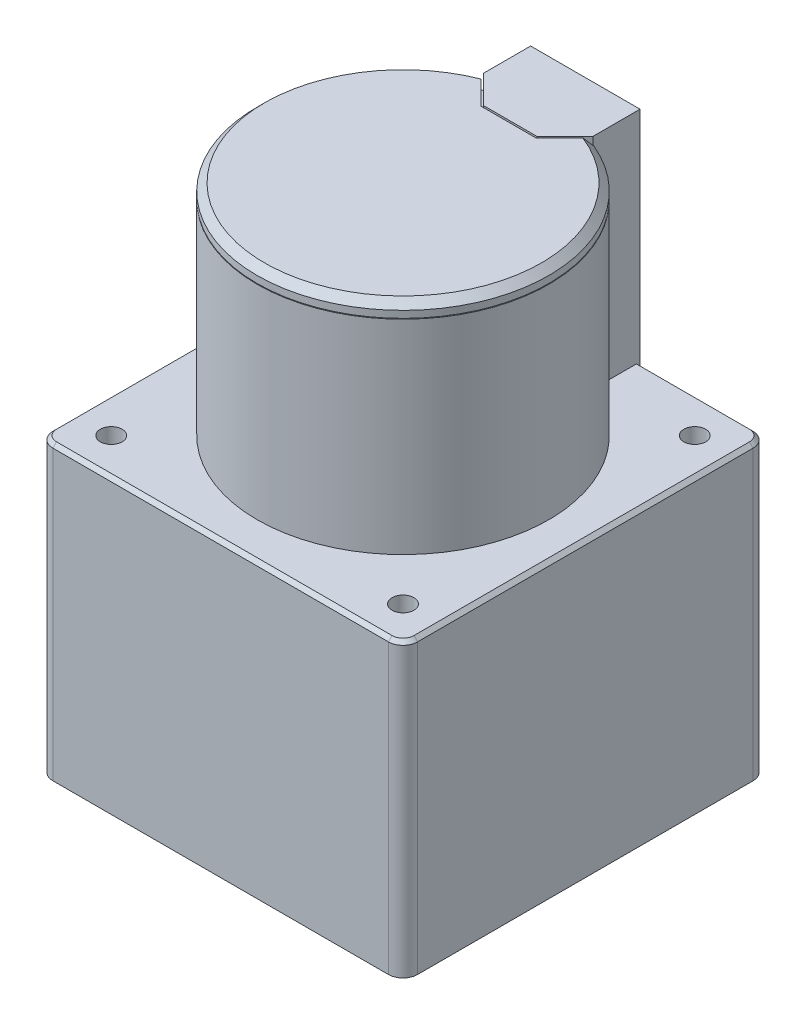
SolidWorks part; units mm, degrees
ref_plane "Front Plane" through (0, 0, 0) normal (0, 0, 1) x (1, 0, 0)
ref_plane "Top Plane" through (0, 0, 0) normal (0, 1, 0) x (1, 0, 0)
ref_plane "Right Plane" through (0, 0, 0) normal (1, 0, 0) x (0, 0, -1)
sketch "Sketch1" plane through (0, 0, 0) normal (0, 1, 0) x (1, 0, 0)
  line L1 (0, 0) -> (50, 0)
  line L2 (0, 0) -> (0, 50)
  line L3 (0, 50) -> (50, 50)
  line L4 (50, 0) -> (50, 50)
  circle A0 centre (5, 45) radius 1.5
  circle A1 centre (45, 45) radius 1.5
  circle A2 centre (5, 5) radius 1.5
  circle A3 centre (45, 5) radius 1.5
  dimension "D3" = 5
  dimension "D4" = 5
  dimension "D5" = 3
  dimension "D6" = 3
  dimension "D7" = 3
  dimension "D8" = 3
  dimension "D9" = 5
  dimension "D10" = 5
  dimension "D11" = 5
  dimension "D12" = 5
  dimension "D13" = 5
  dimension "D14" = 5
  dimension "D1" = 50
  dimension "D2" = 50
extrude "Boss-Extrude1" add sketch "Sketch1" along normal blind 40
sketch "Sketch2" plane through (0, 40, 0) normal (0, 1, 0) x (1, 0, 0)
  line L0 (25, 0) -> (25, 50) construction
  line L1 (0, 0) -> (50, 0) construction
  line L2 (50, 50) -> (0, 50) construction
  line L3 (50, 25) -> (0, 25) construction
  line L4 (50, 0) -> (50, 50) construction
  line L5 (0, 50) -> (0, 0) construction
  line L7 (17.5, 50) -> (32.5, 50)
  line L8 (17.5, 50) -> (17.5, 43.5405)
  line L10 (32.5, 50) -> (32.5, 43.5405)
  arc A0 (17.5, 43.5405) -> (32.5, 43.5405) centre (25, 25) ccw
  dimension "D1" = 40
  dimension "D2" = 7.5
  dimension "D3" = 15
extrude "Boss-Extrude2" add sketch "Sketch2" along normal blind 30
ref_plane "Plane1" through (0, 68, 0) normal (0, 1, 0) x (1, 0, 0)
sketch "Sketch3" plane through (0, 68, 0) normal (0, 1, 0) x (1, 0, 0)
  line L0 (25, 50) -> (25, 0) construction
  line L1 (21, 39.7016) -> (29, 39.7016)
  line L2 (32.5, 50) -> (17.5, 50) construction
  line L3 (17.433, 43.2429) -> (20.8896, 39.4516)
  line L4 (20.8896, 39.4516) -> (29.1104, 39.4516)
  line L5 (29.1104, 39.4516) -> (32.567, 43.2429)
  line L6 (17.5, 43.5405) -> (17.0126, 44.1511)
  line L7 (32.5, 43.5405) -> (32.9874, 44.1511)
  line L8 (0, 0) -> (50, 0) construction
  line L9 (17.5, 43.5405) -> (21, 39.7016)
  line L10 (32.5, 43.5405) -> (29, 39.7016)
  arc A0 (17.433, 43.2429) -> (32.567, 43.2429) centre (25, 25) ccw
  arc A1 (17.0126, 44.1511) -> (32.9874, 44.1511) centre (25, 25) ccw
  dimension "D1" = 39.5
  dimension "D2" = 1
  dimension "D3" = 0.25
  dimension "D4" = 0.25
  dimension "D5" = 8
  dimension "D6" = 0.25
  dimension "D7" = 10.2984
  dimension "D8" = 0.4874
  dimension "D9" = 4
  dimension "D10" = 0.4874
extrude "Cut-Extrude1" cut sketch "Sketch3" against normal mid plane 0.1
sketch "Sketch4" plane through (0, 70, 0) normal (0, 1, 0) x (1, 0, 0)
  line L0 (17.5, 43.5405) -> (21.3405, 39.7)
  line L1 (21.3405, 39.7) -> (28.6595, 39.7)
  line L2 (28.6595, 39.7) -> (32.5, 43.5405)
  line L3 (32.5, 43.5405) -> (32.8536, 43.5405)
  line L4 (32.8536, 43.5405) -> (28.7631, 39.45)
  line L5 (28.7631, 39.45) -> (21.2723, 39.45)
  line L6 (21.2723, 39.45) -> (17.1818, 43.5405)
  line L7 (17.1818, 43.5405) -> (17.5, 43.5405)
  line L8 (32.5, 50) -> (17.5, 50) construction
  dimension "D1" = 10.3
  dimension "D2" = 135
  dimension "D3" = 135
  dimension "D4" = 0.225
  dimension "D5" = 0.25
  dimension "D6" = 0.25
extrude "Cut-Extrude2" cut sketch "Sketch4" against normal up to surface (2.05 mm away) up to face at (25, 67.95, -31.849)
chamfer "Chamfer1" distance 1 angle 45 1 edges at (24.9865, 70, -5)
fillet "Fillet1" radius 2 4 edges at (50, 20, -50) (0, 20, -50) (0, 20, 0) (50, 20, 0)
chamfer "Chamfer3" distance 0.5 angle 45 9 edges at (40.25, 40, -50) (49.4142, 40, -49.4142) (50, 40, -25) (49.4142, 40, -0.5858) (25, 40, 0) (0.5858, 40, -0.5858) (0, 40, -25) (0.5858, 40, -49.4142) (9.75, 40, -50)
